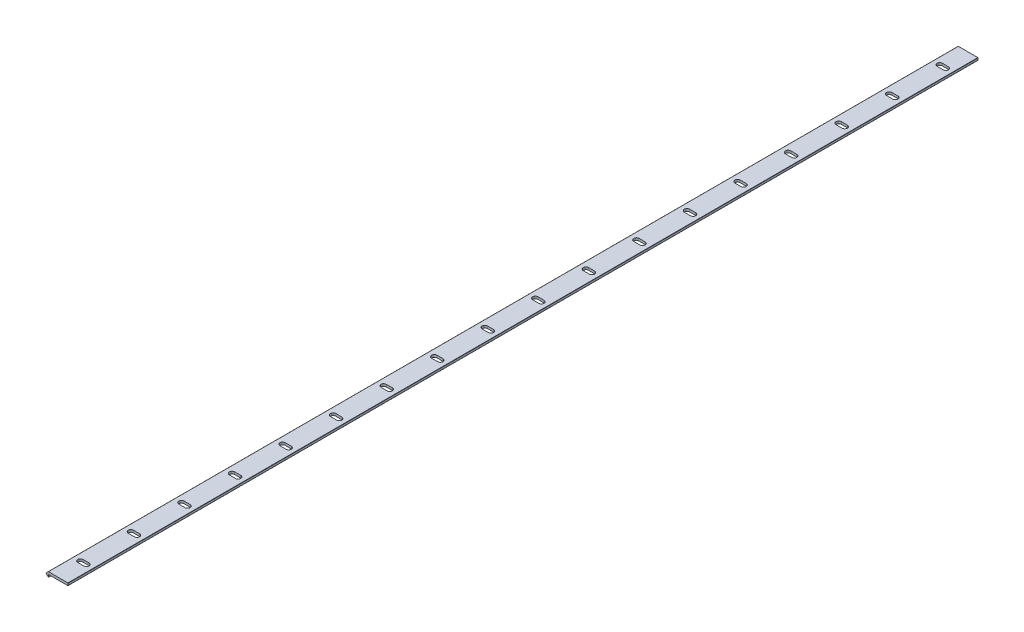
SolidWorks part; units mm, degrees
material "6061 Alloy"
ref_plane "Front Plane" through (0, 0, 0) normal (0, 0, 1) x (1, 0, 0)
ref_plane "Top Plane" through (0, 0, 0) normal (0, 1, 0) x (1, 0, 0)
ref_plane "Right Plane" through (0, 0, 0) normal (1, 0, 0) x (0, 0, -1)
sketch "Sketch1" plane through (0, 0, 0) normal (0, 0, 1) x (1, 0, 0)
  line L0 (0, 0) -> (-19.2062, 0)
  line L1 (-19.5291, 0) -> (-21.9041, -2.375)
  line L2 (-21.9041, -2.375) -> (-19.5291, -4.75)
  line L3 (-19.5291, -4.75) -> (-19.2062, -4.75)
  line L4 (-19.2062, -4.75) -> (-19.2062, -2.375)
  line L5 (-19.2062, -2.375) -> (0, -2.375)
  line L6 (0, -2.375) -> (0, 0)
  line L7 (-19.5291, 0) -> (-19.5291, -4.75) construction
  line L8 (-19.2062, 0) -> (-19.5291, 0)
  line L9 (-19.2062, 0) -> (-19.2062, -2.375) construction
  dimension "D1" = 4.75
  dimension "D2" = 19.5291
  dimension "D3" = 2.6979
  dimension "D4" = 135
extrude "Boss-Extrude1" add sketch "Sketch1" against normal blind 900
fillet "Fillet1" radius 0.2 6 edges at (-19.5291, 0, -450) (-21.9041, -2.375, -450) (0, -2.375, -450) (-19.5291, -4.75, -450) (0, 0, -450) (-19.2062, -4.75, -450)
sketch "Sketch2" plane through (0, 0, 0) normal (0, 1, 0) x (1, 0, 0)
  line L0 (-9.8231, 0) -> (-9.8231, 22.375) construction
  line L1 (-12.8231, 27.625) -> (-6.8231, 27.625)
  line L2 (-12.8231, 27.625) -> (-12.8231, 22.375) construction
  line L3 (-12.8231, 22.375) -> (-6.8231, 22.375)
  line L4 (-6.8231, 27.625) -> (-6.8231, 22.375) construction
  line L5 (-0.2, 0) -> (-19.4463, 0) construction
  line L6 (-6.8231, 25) -> (-12.8231, 25) construction
  arc A0 (-6.8231, 22.375) -> (-6.8231, 27.625) centre (-6.8231, 25) ccw
  arc A1 (-12.8231, 27.625) -> (-12.8231, 22.375) centre (-12.8231, 25) ccw
  dimension "D2" = 5.25
  dimension "D1" = 6
  dimension "D3" = 25
extrude "Cut-Extrude1" cut sketch "Sketch2" against normal up to next (2.375 mm away)
pattern_linear "LPattern1" count 18 spacing 50 along (0, 0, -1) of "Cut-Extrude1"
